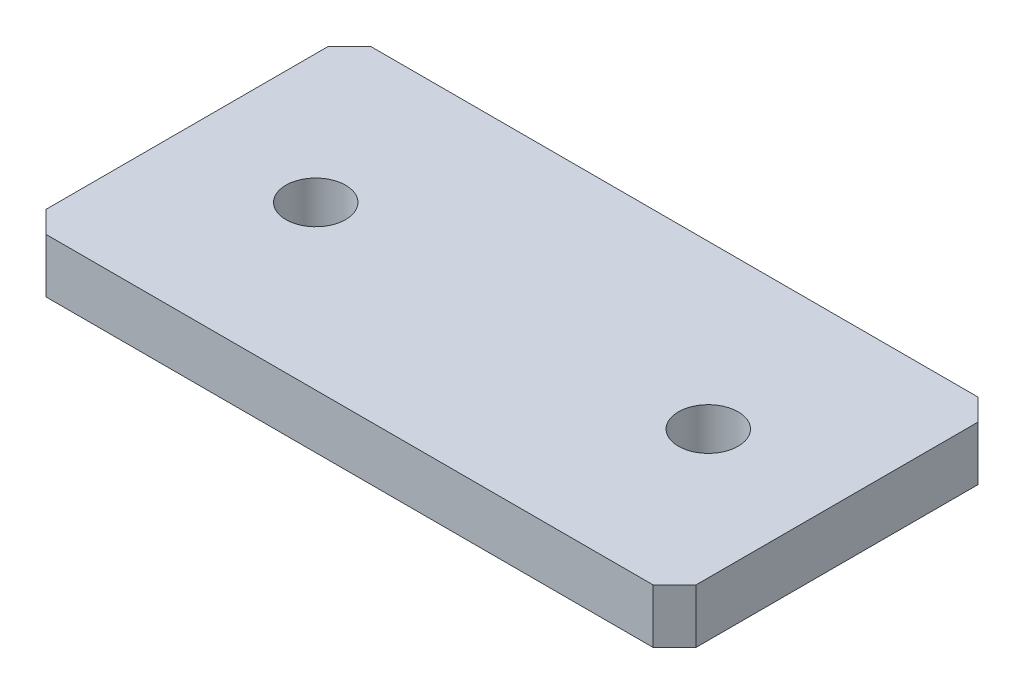
SolidWorks part; units mm, degrees
ref_plane "Front Plane" through (0, 0, 0) normal (0, 0, 1) x (1, 0, 0)
ref_plane "Top Plane" through (0, 0, 0) normal (0, 1, 0) x (1, 0, 0)
ref_plane "Right Plane" through (0, 0, 0) normal (1, 0, 0) x (0, 0, -1)
sketch "Sketch1" plane through (0, 0, 0) normal (0, 1, 0) x (1, 0, 0)
  line L1 (-38.1, 19.05) -> (38.1, 19.05)
  line L2 (-38.1, 19.05) -> (-38.1, -19.05)
  line L3 (-38.1, -19.05) -> (38.1, -19.05)
  line L4 (38.1, 19.05) -> (38.1, -19.05)
  line L5 (-38.1, 19.05) -> (38.1, -19.05) construction
  line L6 (-38.1, -19.05) -> (38.1, 19.05) construction
  point P0 (0, 0)
  dimension "D1" = 76.2
  dimension "D2" = 38.1
extrude "Boss-Extrude1" add sketch "Sketch1" along normal blind 6.35
hole_wizard "M6 Clearance Hole1" positions "Sketch2" profile "Sketch3" hole size "M6" standard "ANSI Metric" end condition through all
sketch "Sketch2" plane through (0, 6.35, 0) normal (0, 1, 0) x (1, 0, 0)
  line L0 (-23, 0) -> (0, 0) construction
  line L1 (0, 0) -> (23, 0) construction
  point P0 (-23, 0)
  point P2 (23, 0)
  dimension "D1" = 46
sketch "Sketch3" plane through (-23, 6.35, 0) normal (1, 0, 0) x (0, 0, 1)
  line L0 (0, 0) -> (0, 6.35)
  line L1 (0, 6.35) -> (3.5, 6.35)
  line L2 (3.5, 6.35) -> (3.5, 0)
  line L5 (3.5, 0) -> (0, 0)
  line L11 (0, -6.35) -> (0, 107.95) construction
  dimension "Thru Hole Dia." = 7
  dimension "Thru Hole Depth" = 6.35
chamfer "Chamfer1" distance 2.54 angle 45 4 edges at (-38.1, 3.175, -19.05) (38.1, 3.175, -19.05) (38.1, 3.175, 19.05) (-38.1, 3.175, 19.05)
equation "\"width\"= 3in"
equation "\"D1@Sketch1\"=\"width\""
equation "\"depth\"= 1.5in"
equation "\"height\"= .25in"
equation "\"D1@Boss-Extrude1\"= \"height\""
equation "\"D2@Sketch1\"= \"depth\""
equation "\"hole_dist\"= 46mm"
equation "\"D1@Sketch2\"=\"hole_dist\""
